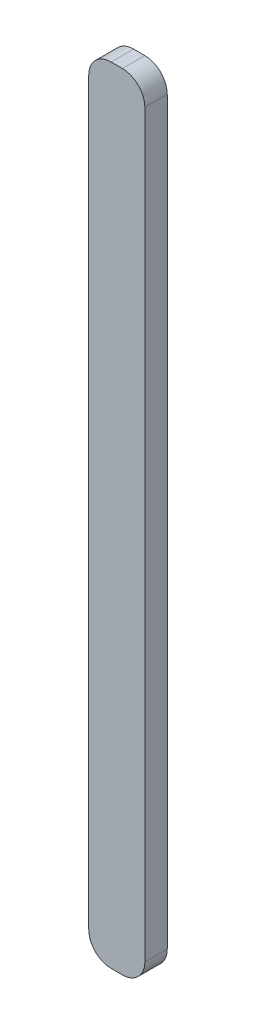
SolidWorks part; units mm, degrees
ref_plane "Front Plane" through (0, 0, 0) normal (0, 0, 1) x (1, 0, 0)
ref_plane "Top Plane" through (0, 0, 0) normal (0, 1, 0) x (1, 0, 0)
ref_plane "Right Plane" through (0, 0, 0) normal (1, 0, 0) x (0, 0, -1)
sketch "Sketch1" plane through (0, 0, 0) normal (0, 0, 1) x (1, 0, 0)
  line L1 (-0.25, 17.5) -> (0.25, 17.5)
  line L2 (-1.25, 16.5) -> (-1.25, -16.5)
  line L3 (-0.25, -17.5) -> (0.25, -17.5)
  line L4 (1.25, 16.5) -> (1.25, -16.5)
  line L5 (-1.25, 17.5) -> (1.25, -17.5) construction
  line L6 (-1.25, -17.5) -> (1.25, 17.5) construction
  arc A0 (0.25, -17.5) -> (1.25, -16.5) centre (0.25, -16.5) ccw
  arc A1 (-1.25, -16.5) -> (-0.25, -17.5) centre (-0.25, -16.5) ccw
  arc A2 (0.25, 17.5) -> (1.25, 16.5) centre (0.25, 16.5) cw
  arc A3 (-0.25, 17.5) -> (-1.25, 16.5) centre (-0.25, 16.5) ccw
  point P0 (0, 0)
  dimension "D3" = 1
  dimension "D1" = 35
  dimension "D2" = 2.5
extrude "Boss-Extrude1" add sketch "Sketch1" along normal blind 1
